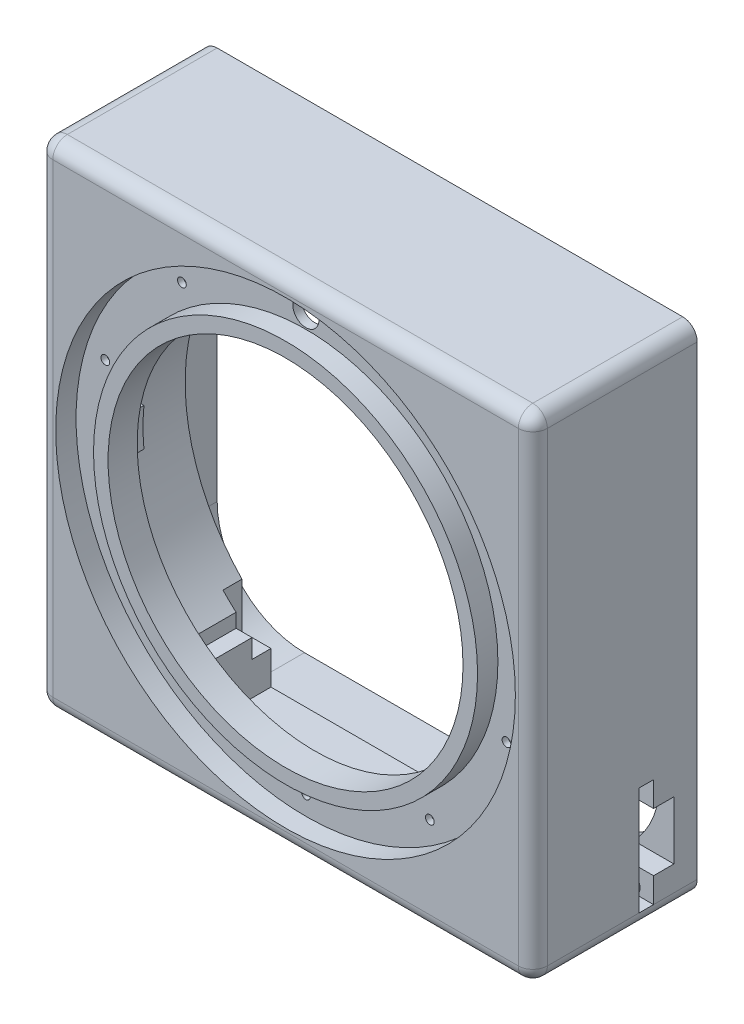
SolidWorks part; units mm, degrees
ref_plane "Plan de face" through (0, 0, 0) normal (0, 0, 1) x (1, 0, 0)
ref_plane "Plan de dessus" through (0, 0, 0) normal (0, 1, 0) x (1, 0, 0)
ref_plane "Plan de droite" through (0, 0, 0) normal (1, 0, 0) x (0, 0, -1)
sketch "Esquisse1" plane through (0, 0, 0) normal (0, 0, 1) x (1, 0, 0)
  line L1 (-42.5, -42.5) -> (42.5, -42.5)
  line L2 (-42.5, -42.5) -> (-42.5, 42.5)
  line L3 (-42.5, 42.5) -> (42.5, 42.5)
  line L4 (42.5, -42.5) -> (42.5, 42.5)
  line L5 (-42.5, -42.5) -> (42.5, 42.5) construction
  line L6 (-42.5, 42.5) -> (42.5, -42.5) construction
  point P0 (0, 0)
  dimension "D1" = 85
  dimension "D2" = 85
extrude "Boss.-Extru.1" add sketch "Esquisse1" along normal blind 5
sketch "Esquisse2" plane through (0, 0, 5) normal (0, 0, 1) x (1, 0, 0)
  circle A0 centre (0, 0) radius 30.5
  dimension "D1" = 61
extrude "Enlèv. mat.-Extru.1" cut sketch "Esquisse2" against normal through all
sketch "Esquisse3" plane through (0, 0, 0) normal (0, 0, -1) x (-1, 0, 0)
  line L0 (-30.5, 0) -> (30.5, 0) construction
  line L1 (-32.3371, 3.25) -> (-42.5, 3.25)
  line L2 (-42.5, -42.5) -> (-42.5, 42.5) construction
  line L3 (-42.5, 3.25) -> (-42.5, -3.25)
  line L4 (-42.5, -3.25) -> (-32.3371, -3.25)
  line L5 (32.3371, -3.25) -> (42.5, -3.25)
  line L6 (42.5, 42.5) -> (42.5, -42.5) construction
  line L7 (42.5, -3.25) -> (42.5, 3.25)
  line L8 (42.5, 3.25) -> (32.3371, 3.25)
  circle A0 centre (0, 0) radius 30.5 construction
  arc A4 (-32.3371, 3.25) -> (-32.3371, -3.25) centre (0, 0) ccw
  arc A5 (32.3371, -3.25) -> (32.3371, 3.25) centre (0, 0) ccw
  point P5 (31.5832, 3.25)
  point P11 (35.75, 0)
  point P16 (31.5832, -3.25)
  point P17 (-31.5832, -3.25)
  point P21 (-31.5832, 3.25)
  point P23 (29.4064, 8.9904)
  dimension "D1" = 6.5
  dimension "D2" = 3.25
  dimension "D3" = 2
extrude "Boss.-Extru.2" add sketch "Esquisse3" along normal blind 3
sketch "Esquisse4" plane through (0, 0, 0) normal (0, 0, -1) x (-1, 0, 0)
  line L0 (-23.5, 29) -> (-20.4756, 29)
  line L1 (-23, -28.5) -> (23, -28.5) construction
  line L2 (-23, -28.5) -> (-23, 28.5) construction
  line L3 (-23, 28.5) -> (23, 28.5) construction
  line L4 (23, -28.5) -> (23, 28.5) construction
  line L5 (-23, -28.5) -> (23, 28.5) construction
  line L6 (-23, 28.5) -> (23, -28.5) construction
  line L7 (23.5, -29) -> (23.5, -26.6083)
  line L8 (-23.5, -29) -> (-20.4756, -29)
  line L9 (-23.5, -29) -> (-23.5, -26.6083)
  line L11 (-42.5, -42.5) -> (42.5, -42.5)
  line L13 (-42.5, 42.5) -> (42.5, 42.5)
  line L15 (-42.5, -42.5) -> (42.5, 42.5) construction
  line L16 (-42.5, 42.5) -> (42.5, -42.5) construction
  line L18 (23.5, 26.6083) -> (23.5, 29)
  line L19 (-23.5, 26.6083) -> (-23.5, 29)
  line L20 (23.5, -29) -> (23.5, 29) construction
  line L21 (20.4756, -29) -> (23.5, -29)
  line L22 (-23.5, -29) -> (-23.5, 29) construction
  line L23 (20.4756, 29) -> (23.5, 29)
  line L24 (-23.5, -29) -> (23.5, -29) construction
  line L25 (-42.5, 42.5) -> (42.5, 42.5) construction
  line L26 (-23.5, 29) -> (23.5, 29) construction
  line L27 (32.3371, -3.25) -> (42.5, -3.25) construction
  line L28 (-42.5, -3.25) -> (-32.3371, -3.25) construction
  line L29 (-42.5, 42.5) -> (-42.5, -42.5)
  line L30 (42.5, 42.5) -> (42.5, -42.5)
  line L31 (42.5, 42.5) -> (42.5, 3.25) construction
  arc A0 (-35.3509, -3.25) -> (-23.5, -26.6083) centre (0, 0) ccw
  arc A1 (35.3509, -3.25) -> (23.5, 26.6083) centre (0, 0) ccw
  arc A2 (-20.4756, -29) -> (20.4756, -29) centre (0, 0) ccw
  arc A3 (23.5, -26.6083) -> (35.3509, -3.25) centre (0, 0) ccw
  arc A4 (20.4756, 29) -> (-20.4756, 29) centre (0, 0) ccw
  arc A5 (-23.5, 26.6083) -> (-35.3509, -3.25) centre (0, 0) ccw
  point P0 (0, 0)
  point P17 (40, 40.7431)
  dimension "D5" = 71
  dimension "D1" = 46
  dimension "D2" = 57
  dimension "D3" = 0.5
extrude "Boss.-Extru.4" add sketch "Esquisse4" along normal blind 10
sketch "Esquisse5" plane through (0, 0, -10) normal (0, 0, -1) x (-1, 0, 0)
  line L0 (14.8387, 32.25) -> (25.75, 32.25)
  line L1 (-25.75, -32.25) -> (-14.8387, -32.25)
  line L2 (-25.75, -32.25) -> (-25.75, -24.4374)
  line L3 (-25.75, 32.25) -> (-14.8387, 32.25)
  line L4 (42.5, -42.5) -> (42.5, 42.5)
  line L5 (42.5, 42.5) -> (-42.5, 42.5)
  line L6 (-42.5, 42.5) -> (-42.5, -42.5)
  line L7 (-42.5, -42.5) -> (42.5, -42.5)
  line L8 (42.5, -42.5) -> (42.5, 42.5)
  line L9 (42.5, 42.5) -> (-42.5, 42.5)
  line L10 (-42.5, 42.5) -> (-42.5, -42.5)
  line L11 (-42.5, -42.5) -> (42.5, -42.5)
  line L12 (25.75, -32.25) -> (25.75, -24.4374)
  line L13 (-25.75, -32.25) -> (25.75, 32.25) construction
  line L14 (-25.75, 32.25) -> (25.75, -32.25) construction
  line L15 (25.75, 24.4374) -> (25.75, 32.25)
  line L16 (14.8387, -32.25) -> (25.75, -32.25)
  line L17 (-25.75, 24.4374) -> (-25.75, 32.25)
  arc A0 (20.4756, 29) -> (-20.4756, 29) centre (0, 0) ccw construction
  arc A1 (14.8387, 32.25) -> (-14.8387, 32.25) centre (0, 0) ccw
  arc A2 (-20.4756, -29) -> (20.4756, -29) centre (0, 0) ccw construction
  arc A3 (-14.8387, -32.25) -> (14.8387, -32.25) centre (0, 0) ccw
  arc A4 (-23.5, 26.6083) -> (-23.5, -26.6083) centre (0, 0) ccw construction
  arc A5 (-25.75, 24.4374) -> (-25.75, -24.4374) centre (0, 0) ccw
  arc A7 (23.5, -26.6083) -> (23.5, 26.6083) centre (0, 0) ccw construction
  arc A8 (25.75, -24.4374) -> (25.75, 24.4374) centre (0, 0) ccw
  point P2 (0, 0)
  dimension "D2" = 51.5
  dimension "D3" = 64.5
  dimension "D1" = 0
extrude "Boss.-Extru.5" add sketch "Esquisse5" along normal blind 3.25
sketch "Esquisse6" plane through (0, 0, 5) normal (0, 0, 1) x (1, 0, 0)
  circle A0 centre (0, 0) radius 33
  circle A1 centre (0, 0) radius 39.5
  circle A2 centre (0, 0) radius 30.5 construction
  dimension "D1" = 6.5
  dimension "D2" = 2.5
extrude "Enlèv. mat.-Extru.2" cut sketch "Esquisse6" against normal blind 3.5
sketch "Esquisse7" plane through (0, 0, -13.25) normal (0, 0, -1) x (-1, 0, 0)
  circle A0 centre (0, 35.5) radius 2.25
  arc A1 (20.4756, 29) -> (-20.4756, 29) centre (0, 0) ccw construction
  dimension "D1" = 4.5
extrude "Enlèv. mat.-Extru.3" cut sketch "Esquisse7" against normal up to surface (14.75 mm away) up to face at (33, 0, 1.5)
sketch "Esquisse8" plane through (0, 0, -13.25) normal (0, 0, -1) x (-1, 0, 0)
  line L0 (-25, 40) -> (25, 40)
  line L1 (-42.5, 42.5) -> (42.5, 42.5)
  line L2 (-42.5, 42.5) -> (-42.5, -42.5)
  line L3 (-42.5, -42.5) -> (42.5, -42.5)
  line L4 (42.5, 42.5) -> (42.5, -42.5)
  line L5 (40, 25) -> (40, -25)
  line L6 (-25, -40) -> (25, -40)
  line L7 (-40, 25) -> (-40, -25)
  line L8 (-40, -40) -> (40, -40) construction
  line L9 (-40, 40) -> (-40, -40) construction
  line L10 (40, 40) -> (40, -40) construction
  line L11 (-40, 40) -> (40, 40) construction
  arc A0 (-25, -40) -> (-40, -25) centre (-25, -25) cw
  arc A1 (40, -25) -> (25, -40) centre (25, -25) cw
  arc A2 (25, 40) -> (40, 25) centre (25, 25) cw
  arc A3 (-25, 40) -> (-40, 25) centre (-25, 25) ccw
  dimension "D2" = 15
  dimension "D1" = 2.5
extrude "Boss.-Extru.6" add sketch "Esquisse8" along normal blind 10
fillet "Congé1" radius 2.5 8 edges at (-42.5, 0, 5) (0, 42.5, 5) (42.5, 0, 5) (0, -42.5, 5) (42.5, -42.5, -9.125) (-42.5, -42.5, -9.125) (-42.5, 42.5, -9.125) (42.5, 42.5, -9.125)
sketch "Esquisse9" plane through (0, 0, -13.25) normal (0, 0, -1) x (-1, 0, 0)
  line L1 (-20.75, -29) -> (20.75, -29)
  line L2 (-20.75, -29) -> (-20.75, -38)
  line L3 (-20.75, -38) -> (20.75, -38)
  line L4 (20.75, -29) -> (20.75, -38)
  line L5 (25.75, -32.25) -> (25.75, -24.4374) construction
  line L6 (-25.75, -24.4374) -> (-25.75, -32.25) construction
  line L7 (-23.5, -29) -> (-20.4756, -29) construction
  point P4 (-20.4756, -29)
  point P5 (-20.4756, -29)
  point P10 (0, 0)
  dimension "D1" = 5
  dimension "D2" = 5
  dimension "D3" = 9
extrude "Enlèv. mat.-Extru.4" cut sketch "Esquisse9" against normal up to surface (13.25 mm away) up to face at (0, 2.9412, 0)
sketch "Esquisse10" plane through (0, 0, 1.5) normal (0, 0, 1) x (1, 0, 0)
  line L0 (0, 0) -> (0, 33) construction
  line L1 (0, 33) -> (0, 39.5) construction
  line L2 (19.3969, 26.6976) -> (23.2175, 31.9562) construction
  line L3 (31.3849, 10.1976) -> (37.5667, 12.2062) construction
  line L4 (31.3849, -10.1976) -> (37.5667, -12.2062) construction
  line L5 (19.3969, -26.6976) -> (23.2175, -31.9562) construction
  line L6 (0, -33) -> (0, -39.5) construction
  line L7 (-19.3969, -26.6976) -> (-23.2175, -31.9562) construction
  line L8 (-31.3849, -10.1976) -> (-37.5667, -12.2062) construction
  line L9 (-31.3849, 10.1976) -> (-37.5667, 12.2062) construction
  line L10 (-19.3969, 26.6976) -> (-23.2175, 31.9562) construction
  circle A1 centre (0, 0) radius 33 construction
  circle A2 centre (0, 0) radius 39.5 construction
  circle A3 centre (0, 36.25) radius 0.75
  circle A4 centre (21.3072, 29.3269) radius 0.75
  circle A5 centre (34.4758, 11.2019) radius 0.75
  circle A6 centre (34.4758, -11.2019) radius 0.75
  circle A7 centre (21.3072, -29.3269) radius 0.75
  circle A8 centre (0, -36.25) radius 0.75
  circle A9 centre (-21.3072, -29.3269) radius 0.75
  circle A10 centre (-34.4758, -11.2019) radius 0.75
  circle A11 centre (-34.4758, 11.2019) radius 0.75
  circle A12 centre (-21.3072, 29.3269) radius 0.75
  point P52 (0, 0)
  dimension "D1" = 1.5
  dimension "D2" = 10
extrude "Enlèv. mat.-Extru.5" cut sketch "Esquisse10" against normal blind 1
sketch "Esquisse11" plane through (0, 0, -23.25) normal (0, 0, -1) x (-1, 0, 0)
  line L0 (35.6066, 35.6066) -> (41.7678, 41.7678) construction
  line L1 (35.6066, -35.6066) -> (41.7678, -41.7678) construction
  line L2 (-35.6066, -35.6066) -> (-41.7678, -41.7678) construction
  line L3 (-35.6066, 35.6066) -> (-41.7678, 41.7678) construction
  arc A0 (40, 25) -> (25, 40) centre (25, 25) ccw construction
  arc A1 (42.5, 40) -> (40, 42.5) centre (40, 40) ccw construction
  circle A2 centre (38.6872, 38.6872) radius 1.5
  circle A3 centre (38.6872, -38.6872) radius 1.5
  circle A4 centre (-38.6872, -38.6872) radius 1.5
  circle A5 centre (-38.6872, 38.6872) radius 1.5
  point P25 (0, 0)
  dimension "D1" = 3
  dimension "D2" = 4
extrude "Enlèv. mat.-Extru.6" cut sketch "Esquisse11" against normal offset from surface (23.25 mm away) 5 up to face at (0, 0, 5)
sketch "Esquisse12" plane through (40, 0, 0) normal (-1, 0, 0) x (0, 0, 1)
  line L0 (-13.25, 25) -> (-13.25, -25) construction
  line L1 (-13.25, -21.4) -> (-15.75, -21.4)
  line L2 (-13.25, -21.4) -> (-13.25, -40)
  line L3 (-13.25, -40) -> (-15.75, -40)
  line L4 (-15.75, -21.4) -> (-15.75, -25.7)
  line L5 (-13.25, -30.7) -> (-29.9654, -30.7) construction
  line L6 (-15.75, -25.7) -> (-19.25, -25.7)
  line L7 (-19.25, -25.7) -> (-19.25, -35.7)
  line L8 (-19.25, -35.7) -> (-15.75, -35.7)
  line L9 (-15.75, -35.7) -> (-15.75, -40)
  line L10 (-23.25, -42.5) -> (2.5, -42.5) construction
  point P11 (-19.25, -30.7)
  dimension "D1" = 18.6
  dimension "D2" = 2.5
  dimension "D3" = 6
  dimension "D4" = 10
  dimension "D5" = 2.5
extrude "Enlèv. mat.-Extru.7" cut sketch "Esquisse12" against normal through all both and the other way through all
equation "\"D2@Esquisse3\"=\"D1@Esquisse3\"/2"
